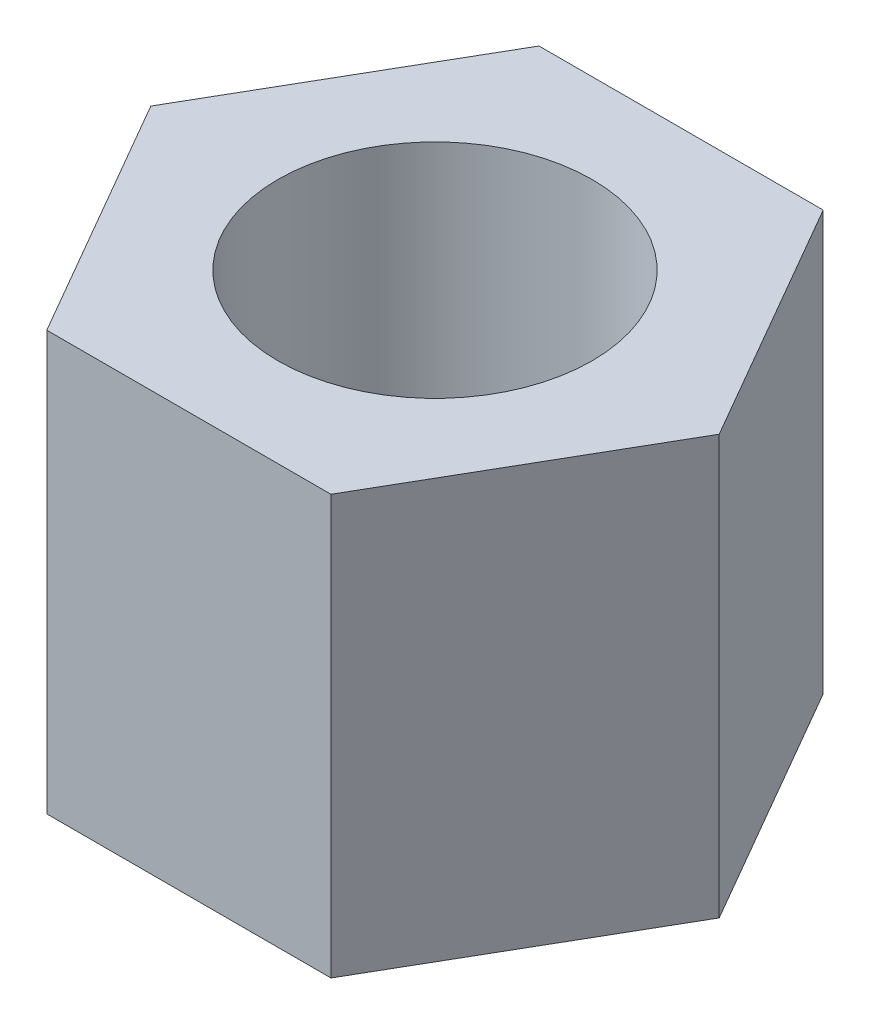
SolidWorks part; units mm, degrees
ref_plane "前视基准面" through (0, 0, 0) normal (0, 0, 1) x (1, 0, 0)
ref_plane "上视基准面" through (0, 0, 0) normal (0, 1, 0) x (1, 0, 0)
ref_plane "右视基准面" through (0, 0, 0) normal (1, 0, 0) x (0, 0, -1)
sketch "草图1" plane through (0, 0, 0) normal (0, 1, 0) x (1, 0, 0)
  line L0 (-1.3568, 2.35) -> (1.3568, 2.35)
  line L1 (1.3568, 2.35) -> (2.7135, 0)
  line L2 (2.7135, 0) -> (1.3568, -2.35)
  line L3 (1.3568, -2.35) -> (-1.3568, -2.35)
  line L4 (-1.3568, -2.35) -> (-2.7135, 0)
  line L5 (-2.7135, 0) -> (-1.3568, 2.35)
  line L6 (-2.7135, 0) -> (2.7135, 0) construction
  line L7 (-1.3568, 2.35) -> (1.3568, -2.35) construction
  circle A0 centre (0, 0) radius 1.5
  point P4 (0, 0)
  dimension "D6" = 3
  dimension "D1" = 4.7
  dimension "D2" = 4.7
  dimension "D3" = 4.7
  dimension "D4" = 120
  dimension "D5" = 120
extrude "凸台-拉伸1" add sketch "草图1" along normal blind 4
